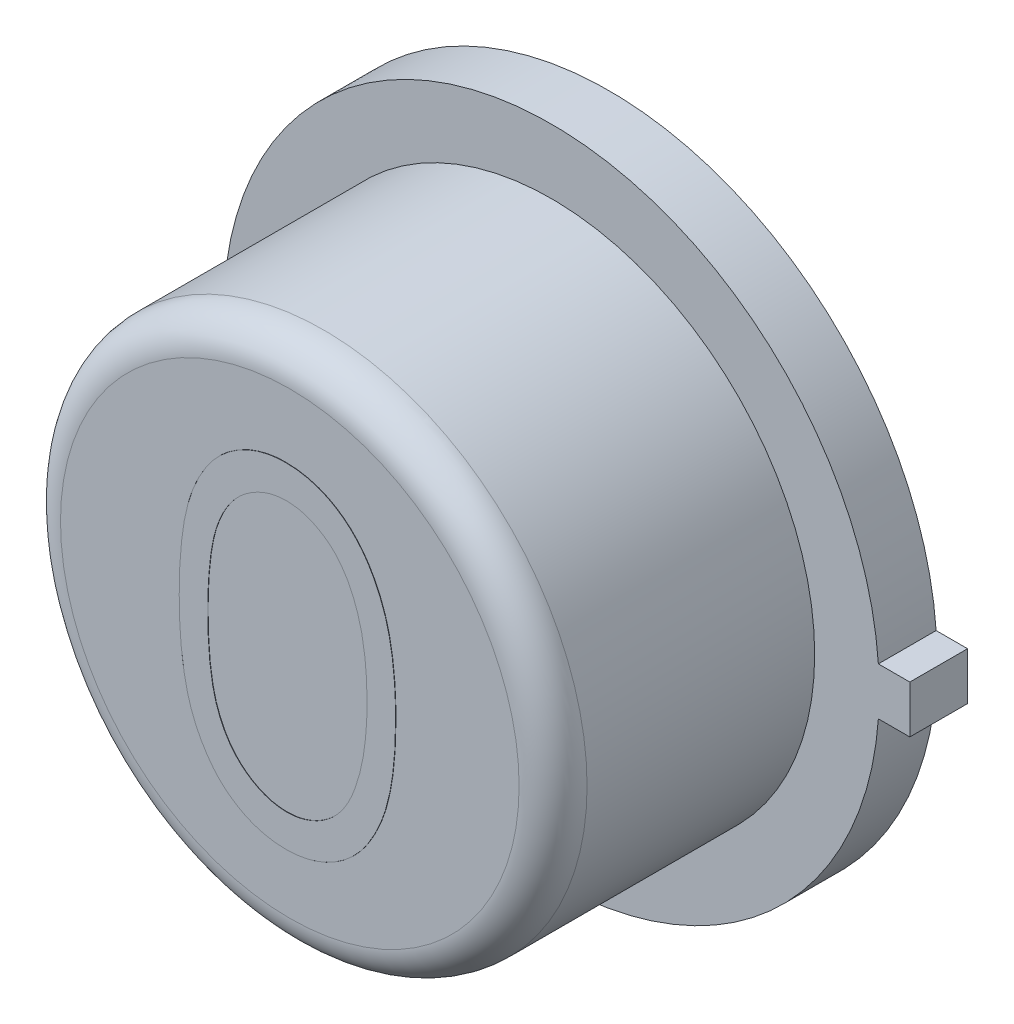
SolidWorks part; units mm, degrees
ref_plane "Front Plane" through (0, 0, 0) normal (0, 0, 1) x (1, 0, 0)
ref_plane "Top Plane" through (0, 0, 0) normal (0, 1, 0) x (1, 0, 0)
ref_plane "Right Plane" through (0, 0, 0) normal (1, 0, 0) x (0, 0, -1)
sketch "Sketch1" plane through (0, 0, 0) normal (0, 0, 1) x (1, 0, 0)
  line L1 (2.4511, 0.1778) -> (2.6797, 0.1778)
  line L3 (2.4511, -0.1778) -> (2.6797, -0.1778)
  line L4 (2.6797, 0.1778) -> (2.6797, -0.1778)
  line L5 (2.4511, 0.1778) -> (2.4444, 0.1778)
  line L6 (2.4511, -0.1778) -> (2.4446, -0.1778)
  arc A0 (2.4446, 0.1778) -> (2.4446, -0.1778) centre (0, 0) ccw
  dimension "D1" = 4.9022
  dimension "D2" = 0.3556
  dimension "D3" = 0.2286
extrude "Boss-Extrude1" add sketch "Sketch1" along normal blind 0.4318
sketch "Sketch2" plane through (0, 0, 0.4318) normal (0, 0, 1) x (1, 0, 0)
  circle A0 centre (0, 0) radius 1.9685
  dimension "D1" = 3.937
extrude "Boss-Extrude2" add sketch "Sketch2" along normal blind 1.9558
sketch "Sketch3" plane through (0, 0, 0) normal (0, 0, -1) x (-1, 0, 0)
  circle A0 centre (0, 0) radius 1.7576
extrude "Boss-Extrude3" add sketch "Sketch3" along normal blind 0.0025
fillet "Fillet1" radius 0.254 1 edges at (1.9685, 0, 2.3876)
sketch "Sketch4" plane through (0, 0, 2.3876) normal (0, 0, 1) x (1, 0, 0)
  line L0 (-1.2065, -1.2181) -> (1.2065, -1.2181) construction
  circle A0 centre (0, 0) radius 1.7145 construction
  text T0 "0" font "Century Gothic" height in points 9
  dimension "D1" = 2.413
extrude "Boss-Extrude6" add sketch "Sketch4" along normal blind 0.0025
